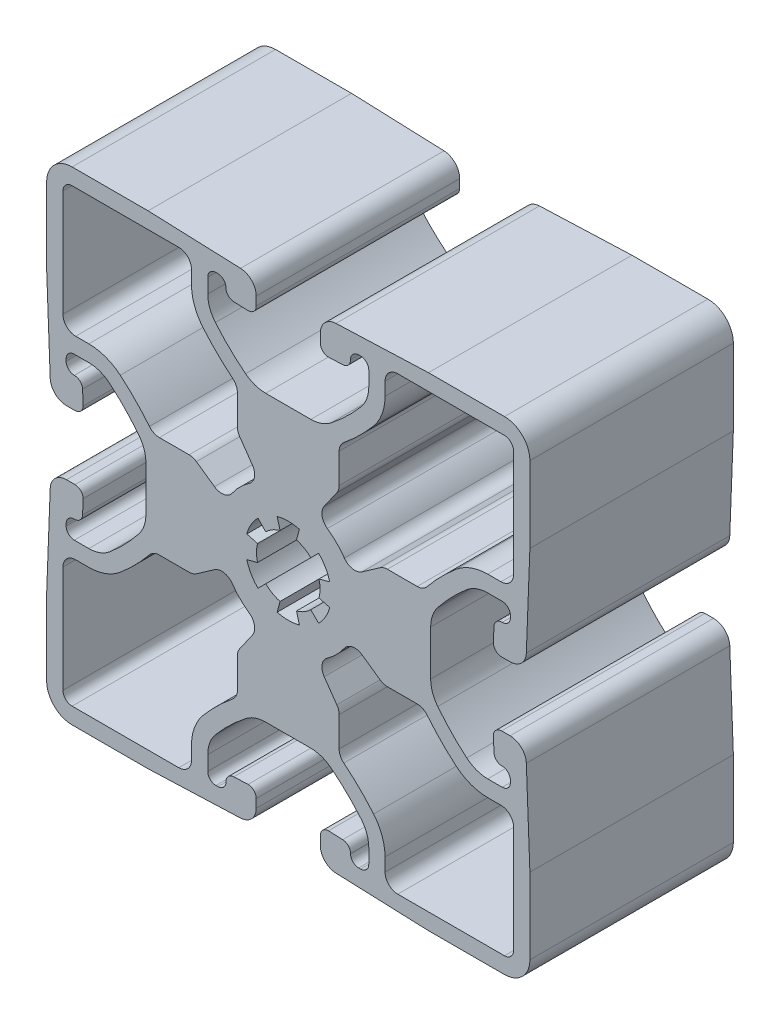
SolidWorks part; units mm, degrees
material "6061 Alloy"
ref_plane "Front" through (0, 0, 0) normal (0, 0, 1) x (1, 0, 0)
ref_plane "Top" through (0, 0, 0) normal (0, 1, 0) x (1, 0, 0)
ref_plane "Right" through (0, 0, 0) normal (1, 0, 0) x (0, 0, -1)
sketch "Sketch1" plane through (0, 0, 0) normal (0, 0, 1) x (1, 0, 0)
  line L0 (11.4645, -6.0629) -> (9.2144, -4.4874)
  line L1 (4.4874, -9.2144) -> (6.0629, -11.4645)
  line L2 (16.0992, -6.35) -> (12.375, -6.35)
  line L3 (6.35, -12.375) -> (6.35, -16.0931)
  line L4 (26.543, -12.0821) -> (24.8992, -12.0821)
  line L5 (12.0821, -24.8992) -> (12.0821, -26.543)
  line L6 (28.1305, -26.9875) -> (28.1305, -13.6696)
  line L7 (13.6696, -28.1305) -> (26.9875, -28.1305)
  line L8 (-6.35, -16.0931) -> (-6.35, -12.375)
  line L9 (-6.0629, -11.4645) -> (-4.4874, -9.2144)
  line L10 (-12.0821, -26.543) -> (-12.0821, -24.8992)
  line L11 (-26.9875, -28.1305) -> (-13.6696, -28.1305)
  line L12 (-9.2144, -4.4874) -> (-11.4645, -6.0629)
  line L13 (-28.1305, -13.6696) -> (-28.1305, -26.9875)
  line L14 (-12.375, -6.35) -> (-16.0992, -6.35)
  line L15 (-24.8992, -12.0821) -> (-26.543, -12.0821)
  line L16 (6.0629, 11.4645) -> (4.4874, 9.2144)
  line L17 (9.2144, 4.4874) -> (11.4645, 6.0629)
  line L18 (6.35, 16.0992) -> (6.35, 12.375)
  line L19 (12.375, 6.35) -> (16.0931, 6.35)
  line L20 (12.0821, 26.543) -> (12.0821, 24.8992)
  line L21 (24.8992, 12.0821) -> (26.543, 12.0821)
  line L22 (26.9875, 28.1305) -> (13.6696, 28.1305)
  line L23 (28.1305, 13.6696) -> (28.1305, 26.9875)
  line L24 (5.1768, -1.3871) -> (3.8335, -1.0272)
  line L25 (3.8335, 1.0272) -> (5.1768, 1.3871)
  line L26 (2.8063, -2.8063) -> (3.7897, -3.7897)
  line L27 (3.7897, 3.7897) -> (2.8063, 2.8063)
  line L28 (1.3871, -5.1768) -> (1.0272, -3.8335)
  line L29 (1.0272, 3.8335) -> (1.3871, 5.1768)
  line L30 (-1.0272, -3.8335) -> (-1.3871, -5.1768)
  line L31 (-1.3871, 5.1768) -> (-1.0272, 3.8335)
  line L32 (-3.7897, -3.7897) -> (-2.8063, -2.8063)
  line L33 (-2.8063, 2.8063) -> (-3.7897, 3.7897)
  line L34 (-3.8335, -1.0272) -> (-5.1768, -1.3871)
  line L35 (-5.1768, 1.3871) -> (-3.8335, 1.0272)
  line L36 (-26.9875, 30.1625) -> (-17.5006, 30.1625)
  line L37 (-17.5006, 30.1625) -> (-5.9545, 29.7189)
  line L38 (-30.1625, 17.5006) -> (-30.1625, 26.9875)
  line L39 (-4.0005, 27.6884) -> (-4.0005, 26.6248)
  line L40 (-29.7189, 5.9545) -> (-30.1625, 17.5006)
  line L41 (-5.0165, 25.6088) -> (-6.7982, 25.6772)
  line L42 (-26.6248, 4.0005) -> (-27.6884, 4.0005)
  line L43 (-7.7752, 26.6925) -> (-7.7752, 26.7156)
  line L44 (-25.6772, 6.7982) -> (-25.6088, 5.0165)
  line L45 (-8.7912, 27.7316) -> (-9.0341, 27.7316)
  line L46 (-26.7156, 7.7752) -> (-26.6925, 7.7752)
  line L47 (-10.0501, 26.7156) -> (-10.0501, 24.8992)
  line L48 (-27.7316, 9.0341) -> (-27.7316, 8.7912)
  line L49 (-24.8992, 10.0501) -> (-26.7156, 10.0501)
  line L50 (-2.8198, 17.775) -> (2.8198, 17.775)
  line L51 (-17.775, -2.8198) -> (-17.775, 2.8117)
  line L52 (10.0501, 24.8992) -> (10.0501, 26.7156)
  line L53 (9.0341, 27.7316) -> (8.7912, 27.7316)
  line L54 (-26.7156, -10.0501) -> (-24.8992, -10.0501)
  line L55 (7.7752, 26.7156) -> (7.7752, 26.6925)
  line L56 (-27.7316, -8.7912) -> (-27.7316, -9.0341)
  line L57 (6.7982, 25.6772) -> (5.0165, 25.6088)
  line L58 (-26.6925, -7.7752) -> (-26.7156, -7.7752)
  line L59 (4.0005, 26.6248) -> (4.0005, 27.6884)
  line L60 (-25.6088, -5.0165) -> (-25.6772, -6.7982)
  line L61 (5.9545, 29.7189) -> (17.5006, 30.1625)
  line L62 (-27.6884, -4.0005) -> (-26.6248, -4.0005)
  line L63 (17.5006, 30.1625) -> (26.9875, 30.1625)
  line L64 (-30.1625, -17.5006) -> (-29.7189, -5.9545)
  line L65 (30.1625, 26.9875) -> (30.1625, 17.5006)
  line L66 (-30.1625, -26.9875) -> (-30.1625, -17.5006)
  line L67 (30.1625, 17.5006) -> (29.7189, 5.9545)
  line L68 (-17.5006, -30.1625) -> (-26.9875, -30.1625)
  line L69 (27.6884, 4.0005) -> (26.6248, 4.0005)
  line L70 (-5.9545, -29.7189) -> (-17.5006, -30.1625)
  line L71 (25.6088, 5.0165) -> (25.6772, 6.7982)
  line L72 (-4.0005, -26.6248) -> (-4.0005, -27.6884)
  line L73 (26.6925, 7.7752) -> (26.7156, 7.7752)
  line L74 (-6.7982, -25.6772) -> (-5.0165, -25.6088)
  line L75 (27.7316, 8.7912) -> (27.7316, 9.0341)
  line L76 (-7.7752, -26.7156) -> (-7.7752, -26.6925)
  line L77 (26.7156, 10.0501) -> (24.8992, 10.0501)
  line L78 (-9.0341, -27.7316) -> (-8.7912, -27.7316)
  line L79 (-10.0501, -24.8992) -> (-10.0501, -26.7156)
  line L80 (17.775, 2.8117) -> (17.775, -2.8198)
  line L81 (2.8117, -17.775) -> (-2.8117, -17.775)
  line L82 (24.8992, -10.0501) -> (26.7156, -10.0501)
  line L83 (27.7316, -9.0341) -> (27.7316, -8.7912)
  line L84 (10.0501, -26.7156) -> (10.0501, -24.8992)
  line L85 (26.7156, -7.7752) -> (26.6925, -7.7752)
  line L86 (8.7912, -27.7316) -> (9.0341, -27.7316)
  line L87 (25.6772, -6.7982) -> (25.6088, -5.0165)
  line L88 (7.7752, -26.6925) -> (7.7752, -26.7156)
  line L89 (26.6248, -4.0005) -> (27.6884, -4.0005)
  line L90 (5.0165, -25.6088) -> (6.7982, -25.6772)
  line L91 (29.7189, -5.9545) -> (30.1625, -17.5006)
  line L92 (4.0005, -27.6884) -> (4.0005, -26.6248)
  line L93 (30.1625, -17.5006) -> (30.1625, -26.9875)
  line L94 (17.5006, -30.1625) -> (5.9545, -29.7189)
  line L95 (26.9875, -30.1625) -> (17.5006, -30.1625)
  line L96 (-26.543, 12.0821) -> (-24.8992, 12.0821)
  line L97 (-16.0931, 6.35) -> (-12.375, 6.35)
  line L98 (-28.1305, 26.9875) -> (-28.1305, 13.6696)
  line L99 (-11.4645, 6.0629) -> (-9.2144, 4.4874)
  line L100 (-13.6696, 28.1305) -> (-26.9875, 28.1305)
  line L101 (-12.0821, 24.8992) -> (-12.0821, 26.543)
  line L102 (-4.4874, 9.2144) -> (-6.0629, 11.4645)
  line L103 (-6.35, 12.375) -> (-6.35, 16.0992)
  arc A0 (4.8801, -7.0015) -> (7.0015, -4.8801) centre (0, 0) ccw
  arc A1 (9.2144, -4.4874) -> (7.0015, -4.8801) centre (8.3039, -5.7878) ccw
  arc A2 (4.8801, -7.0015) -> (4.4874, -9.2144) centre (5.7878, -8.3039) ccw
  arc A3 (11.4645, -6.0629) -> (12.375, -6.35) centre (12.375, -4.7625) ccw
  arc A4 (6.35, -12.375) -> (6.0629, -11.4645) centre (4.7625, -12.375) ccw
  arc A5 (17.3327, -6.9382) -> (16.0992, -6.35) centre (16.0992, -7.9375) ccw
  arc A6 (6.35, -16.0931) -> (6.9373, -17.3259) centre (7.9375, -16.0931) ccw
  arc A7 (17.3327, -6.9382) -> (20.971, -10.6477) centre (38.648, 10.3295) ccw
  arc A8 (10.6523, -20.9765) -> (6.9373, -17.3259) centre (-10.3456, -38.6288) ccw
  arc A9 (20.971, -10.6477) -> (24.8992, -12.0821) centre (24.8992, -5.9861) ccw
  arc A10 (12.0821, -24.8992) -> (10.6523, -20.9765) centre (5.9861, -24.8992) ccw
  arc A11 (28.1305, -13.6696) -> (26.543, -12.0821) centre (26.543, -13.6696) ccw
  arc A12 (12.0821, -26.543) -> (13.6696, -28.1305) centre (13.6696, -26.543) ccw
  arc A13 (26.9875, -28.1305) -> (28.1305, -26.9875) centre (26.9875, -26.9875) ccw
  arc A14 (-6.9382, -17.3327) -> (-6.35, -16.0931) centre (-7.9375, -16.0992) ccw
  arc A15 (-6.0629, -11.4645) -> (-6.35, -12.375) centre (-4.7625, -12.375) ccw
  arc A16 (-6.9382, -17.3327) -> (-10.6477, -20.971) centre (10.3295, -38.648) ccw
  arc A17 (-10.6477, -20.971) -> (-12.0821, -24.8992) centre (-5.9861, -24.8992) ccw
  arc A18 (-4.4874, -9.2144) -> (-4.8801, -7.0015) centre (-5.7878, -8.3039) ccw
  arc A19 (-7.0015, -4.8801) -> (-4.8801, -7.0015) centre (0, 0) ccw
  arc A20 (-13.6696, -28.1305) -> (-12.0821, -26.543) centre (-13.6696, -26.543) ccw
  arc A21 (-7.0015, -4.8801) -> (-9.2144, -4.4874) centre (-8.3039, -5.7878) ccw
  arc A22 (-28.1305, -26.9875) -> (-26.9875, -28.1305) centre (-26.9875, -26.9875) ccw
  arc A23 (-12.375, -6.35) -> (-11.4645, -6.0629) centre (-12.375, -4.7625) ccw
  arc A24 (-26.543, -12.0821) -> (-28.1305, -13.6696) centre (-26.543, -13.6696) ccw
  arc A25 (-16.0992, -6.35) -> (-17.3259, -6.9373) centre (-16.0931, -7.9375) ccw
  arc A26 (-20.9765, -10.6523) -> (-17.3259, -6.9373) centre (-38.6288, 10.3456) ccw
  arc A27 (-24.8992, -12.0821) -> (-20.9765, -10.6523) centre (-24.8992, -5.9861) ccw
  arc A28 (7.0015, 4.8801) -> (4.8801, 7.0015) centre (0, 0) ccw
  arc A29 (4.4874, 9.2144) -> (4.8801, 7.0015) centre (5.7878, 8.3039) ccw
  arc A30 (7.0015, 4.8801) -> (9.2144, 4.4874) centre (8.3039, 5.7878) ccw
  arc A31 (6.0629, 11.4645) -> (6.35, 12.375) centre (4.7625, 12.375) ccw
  arc A32 (12.375, 6.35) -> (11.4645, 6.0629) centre (12.375, 4.7625) ccw
  arc A33 (6.9382, 17.3327) -> (6.35, 16.0992) centre (7.9375, 16.0992) ccw
  arc A34 (16.0931, 6.35) -> (17.3259, 6.9373) centre (16.0931, 7.9375) ccw
  arc A35 (6.9382, 17.3327) -> (10.6477, 20.971) centre (-10.3295, 38.648) ccw
  arc A36 (20.9765, 10.6523) -> (17.3259, 6.9373) centre (38.6288, -10.3456) ccw
  arc A37 (10.6477, 20.971) -> (12.0821, 24.8992) centre (5.9861, 24.8992) ccw
  arc A38 (24.8992, 12.0821) -> (20.9765, 10.6523) centre (24.8992, 5.9861) ccw
  arc A39 (13.6696, 28.1305) -> (12.0821, 26.543) centre (13.6696, 26.543) ccw
  arc A40 (26.543, 12.0821) -> (28.1305, 13.6696) centre (26.543, 13.6696) ccw
  arc A41 (28.1305, 26.9875) -> (26.9875, 28.1305) centre (26.9875, 26.9875) ccw
  arc A42 (3.8335, -1.0272) -> (3.8335, 1.0272) centre (0, 0) ccw
  arc A43 (3.7897, -3.7897) -> (5.1768, -1.3871) centre (0, 0) ccw
  arc A44 (5.1768, 1.3871) -> (3.7897, 3.7897) centre (0, 0) ccw
  arc A45 (1.0272, -3.8335) -> (2.8063, -2.8063) centre (0, 0) ccw
  arc A46 (2.8063, 2.8063) -> (1.0272, 3.8335) centre (0, 0) ccw
  arc A47 (-1.3871, -5.1768) -> (1.3871, -5.1768) centre (0, 0) ccw
  arc A48 (1.3871, 5.1768) -> (-1.3871, 5.1768) centre (0, 0) ccw
  arc A49 (-2.8063, -2.8063) -> (-1.0272, -3.8335) centre (0, 0) ccw
  arc A50 (-1.0272, 3.8335) -> (-2.8063, 2.8063) centre (0, 0) ccw
  arc A51 (-5.1768, -1.3871) -> (-3.7897, -3.7897) centre (0, 0) ccw
  arc A52 (-3.7897, 3.7897) -> (-5.1768, 1.3871) centre (0, 0) ccw
  arc A53 (-3.8335, 1.0272) -> (-3.8335, -1.0272) centre (0, 0) ccw
  arc A54 (-26.9875, 30.1625) -> (-30.1625, 26.9875) centre (-26.9875, 26.9875) ccw
  arc A55 (-4.0005, 27.6884) -> (-5.9545, 29.7189) centre (-6.0325, 27.6884) ccw
  arc A56 (-5.0165, 25.6088) -> (-4.0005, 26.6248) centre (-5.0165, 26.6248) ccw
  arc A57 (-29.7189, 5.9545) -> (-27.6884, 4.0005) centre (-27.6884, 6.0325) ccw
  arc A58 (-7.7752, 26.6925) -> (-6.7982, 25.6772) centre (-6.7592, 26.6925) ccw
  arc A59 (-26.6248, 4.0005) -> (-25.6088, 5.0165) centre (-26.6248, 5.0165) ccw
  arc A60 (-7.7752, 26.7156) -> (-8.7912, 27.7316) centre (-8.7912, 26.7156) ccw
  arc A61 (-25.6772, 6.7982) -> (-26.6925, 7.7752) centre (-26.6925, 6.7592) ccw
  arc A62 (-9.0341, 27.7316) -> (-10.0501, 26.7156) centre (-9.0341, 26.7156) ccw
  arc A63 (-27.7316, 8.7912) -> (-26.7156, 7.7752) centre (-26.7156, 8.7912) ccw
  arc A64 (-10.0501, 24.8992) -> (-9.0969, 22.2841) centre (-5.9861, 24.8992) ccw
  arc A65 (-26.7156, 10.0501) -> (-27.7316, 9.0341) centre (-26.7156, 9.0341) ccw
  arc A66 (-9.0969, 22.2841) -> (-5.3275, 18.641) centre (10.3456, 38.6288) ccw
  arc A67 (-5.3275, 18.641) -> (-2.8198, 17.775) centre (-2.8198, 21.839) ccw
  arc A68 (-22.2804, 9.0938) -> (-24.8992, 10.0501) centre (-24.8992, 5.9861) ccw
  arc A69 (-18.6606, 5.3442) -> (-22.2804, 9.0938) centre (-38.648, -10.3295) ccw
  arc A70 (2.8198, 17.775) -> (5.3442, 18.6606) centre (2.8116, 21.839) ccw
  arc A71 (-17.775, 2.8117) -> (-18.6606, 5.3442) centre (-21.839, 2.8117) ccw
  arc A72 (5.3442, 18.6606) -> (9.0938, 22.2804) centre (-10.3295, 38.648) ccw
  arc A73 (9.0938, 22.2804) -> (10.0501, 24.8992) centre (5.9861, 24.8992) ccw
  arc A74 (-18.641, -5.3275) -> (-17.775, -2.8198) centre (-21.839, -2.8198) ccw
  arc A75 (-22.2841, -9.0969) -> (-18.641, -5.3275) centre (-38.6288, 10.3456) ccw
  arc A76 (10.0501, 26.7156) -> (9.0341, 27.7316) centre (9.0341, 26.7156) ccw
  arc A77 (-24.8992, -10.0501) -> (-22.2841, -9.0969) centre (-24.8992, -5.9861) ccw
  arc A78 (8.7912, 27.7316) -> (7.7752, 26.7156) centre (8.7912, 26.7156) ccw
  arc A79 (-27.7316, -9.0341) -> (-26.7156, -10.0501) centre (-26.7156, -9.0341) ccw
  arc A80 (6.7982, 25.6772) -> (7.7752, 26.6925) centre (6.7592, 26.6925) ccw
  arc A81 (-26.7156, -7.7752) -> (-27.7316, -8.7912) centre (-26.7156, -8.7912) ccw
  arc A82 (4.0005, 26.6248) -> (5.0165, 25.6088) centre (5.0165, 26.6248) ccw
  arc A83 (-26.6925, -7.7752) -> (-25.6772, -6.7982) centre (-26.6925, -6.7592) ccw
  arc A84 (5.9545, 29.7189) -> (4.0005, 27.6884) centre (6.0325, 27.6884) ccw
  arc A85 (-25.6088, -5.0165) -> (-26.6248, -4.0005) centre (-26.6248, -5.0165) ccw
  arc A86 (-27.6884, -4.0005) -> (-29.7189, -5.9545) centre (-27.6884, -6.0325) ccw
  arc A87 (30.1625, 26.9875) -> (26.9875, 30.1625) centre (26.9875, 26.9875) ccw
  arc A88 (-30.1625, -26.9875) -> (-26.9875, -30.1625) centre (-26.9875, -26.9875) ccw
  arc A89 (27.6884, 4.0005) -> (29.7189, 5.9545) centre (27.6884, 6.0325) ccw
  arc A90 (25.6088, 5.0165) -> (26.6248, 4.0005) centre (26.6248, 5.0165) ccw
  arc A91 (-5.9545, -29.7189) -> (-4.0005, -27.6884) centre (-6.0325, -27.6884) ccw
  arc A92 (26.6925, 7.7752) -> (25.6772, 6.7982) centre (26.6925, 6.7592) ccw
  arc A93 (-4.0005, -26.6248) -> (-5.0165, -25.6088) centre (-5.0165, -26.6248) ccw
  arc A94 (26.7156, 7.7752) -> (27.7316, 8.7912) centre (26.7156, 8.7912) ccw
  arc A95 (-6.7982, -25.6772) -> (-7.7752, -26.6925) centre (-6.7592, -26.6925) ccw
  arc A96 (27.7316, 9.0341) -> (26.7156, 10.0501) centre (26.7156, 9.0341) ccw
  arc A97 (-8.7912, -27.7316) -> (-7.7752, -26.7156) centre (-8.7912, -26.7156) ccw
  arc A98 (24.8992, 10.0501) -> (22.2841, 9.0969) centre (24.8992, 5.9861) ccw
  arc A99 (-10.0501, -26.7156) -> (-9.0341, -27.7316) centre (-9.0341, -26.7156) ccw
  arc A100 (22.2841, 9.0969) -> (18.641, 5.3275) centre (38.6288, -10.3456) ccw
  arc A101 (18.641, 5.3275) -> (17.775, 2.8117) centre (21.839, 2.8198) ccw
  arc A102 (-9.0938, -22.2804) -> (-10.0501, -24.8992) centre (-5.9861, -24.8992) ccw
  arc A103 (-5.3442, -18.6606) -> (-9.0938, -22.2804) centre (10.3295, -38.648) ccw
  arc A104 (17.775, -2.8198) -> (18.6606, -5.3442) centre (21.839, -2.8116) ccw
  arc A105 (-2.8117, -17.775) -> (-5.3442, -18.6606) centre (-2.8117, -21.839) ccw
  arc A106 (18.6606, -5.3442) -> (22.2804, -9.0938) centre (38.648, 10.3295) ccw
  arc A107 (22.2804, -9.0938) -> (24.8992, -10.0501) centre (24.8992, -5.9861) ccw
  arc A108 (5.3275, -18.641) -> (2.8117, -17.775) centre (2.8198, -21.839) ccw
  arc A109 (9.0969, -22.2841) -> (5.3275, -18.641) centre (-10.3456, -38.6288) ccw
  arc A110 (26.7156, -10.0501) -> (27.7316, -9.0341) centre (26.7156, -9.0341) ccw
  arc A111 (10.0501, -24.8992) -> (9.0969, -22.2841) centre (5.9861, -24.8992) ccw
  arc A112 (27.7316, -8.7912) -> (26.7156, -7.7752) centre (26.7156, -8.7912) ccw
  arc A113 (9.0341, -27.7316) -> (10.0501, -26.7156) centre (9.0341, -26.7156) ccw
  arc A114 (25.6772, -6.7982) -> (26.6925, -7.7752) centre (26.6925, -6.7592) ccw
  arc A115 (7.7752, -26.7156) -> (8.7912, -27.7316) centre (8.7912, -26.7156) ccw
  arc A116 (26.6248, -4.0005) -> (25.6088, -5.0165) centre (26.6248, -5.0165) ccw
  arc A117 (7.7752, -26.6925) -> (6.7982, -25.6772) centre (6.7592, -26.6925) ccw
  arc A118 (29.7189, -5.9545) -> (27.6884, -4.0005) centre (27.6884, -6.0325) ccw
  arc A119 (5.0165, -25.6088) -> (4.0005, -26.6248) centre (5.0165, -26.6248) ccw
  arc A120 (4.0005, -27.6884) -> (5.9545, -29.7189) centre (6.0325, -27.6884) ccw
  arc A121 (26.9875, -30.1625) -> (30.1625, -26.9875) centre (26.9875, -26.9875) ccw
  arc A122 (-17.3327, 6.9382) -> (-20.971, 10.6477) centre (-38.648, -10.3295) ccw
  arc A123 (-20.971, 10.6477) -> (-24.8992, 12.0821) centre (-24.8992, 5.9861) ccw
  arc A124 (-17.3327, 6.9382) -> (-16.0931, 6.35) centre (-16.0992, 7.9375) ccw
  arc A125 (-28.1305, 13.6696) -> (-26.543, 12.0821) centre (-26.543, 13.6696) ccw
  arc A126 (-11.4645, 6.0629) -> (-12.375, 6.35) centre (-12.375, 4.7625) ccw
  arc A127 (-26.9875, 28.1305) -> (-28.1305, 26.9875) centre (-26.9875, 26.9875) ccw
  arc A128 (-9.2144, 4.4874) -> (-7.0015, 4.8801) centre (-8.3039, 5.7878) ccw
  arc A129 (-4.8801, 7.0015) -> (-7.0015, 4.8801) centre (0, 0) ccw
  arc A130 (-12.0821, 26.543) -> (-13.6696, 28.1305) centre (-13.6696, 26.543) ccw
  arc A131 (-4.8801, 7.0015) -> (-4.4874, 9.2144) centre (-5.7878, 8.3039) ccw
  arc A132 (-12.0821, 24.8992) -> (-10.6523, 20.9765) centre (-5.9861, 24.8992) ccw
  arc A133 (-6.35, 12.375) -> (-6.0629, 11.4645) centre (-4.7625, 12.375) ccw
  arc A134 (-10.6523, 20.9765) -> (-6.9373, 17.3259) centre (10.3456, 38.6288) ccw
  arc A135 (-6.35, 16.0992) -> (-6.9373, 17.3259) centre (-7.9375, 16.0931) ccw
extrude "Extrude1" add sketch "Sketch1" along normal blind 25.4
